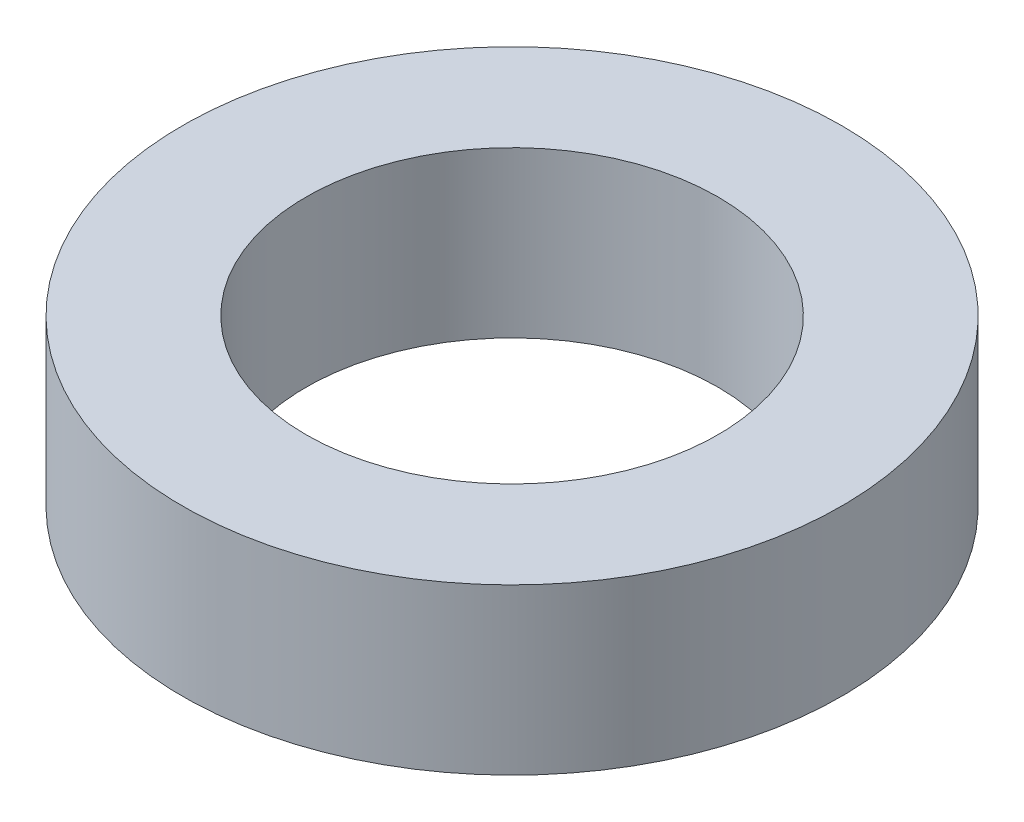
SolidWorks part; units mm, degrees
ref_plane "Спереди" through (0, 0, 0) normal (0, 0, 1) x (1, 0, 0)
ref_plane "Сверху" through (0, 0, 0) normal (0, 1, 0) x (1, 0, 0)
ref_plane "Справа" through (0, 0, 0) normal (1, 0, 0) x (0, 0, -1)
sketch "Эскиз1" plane through (0, 0, 0) normal (0, 0, 1) x (1, 0, 0)
  line L0 (0, 0) -> (0, 17.3309) construction
  line L1 (2.25, 0) -> (3.6, 0)
  line L2 (3.6, 0) -> (3.6, 1.8)
  line L3 (3.6, 1.8) -> (2.25, 1.8)
  line L4 (2.25, 1.8) -> (2.25, 0)
  dimension "D1" = 4.5
  dimension "D2" = 7.2
  dimension "D3" = 1.8
revolve "Повернуть1" add sketch "Эскиз1" angle 360 about L0
